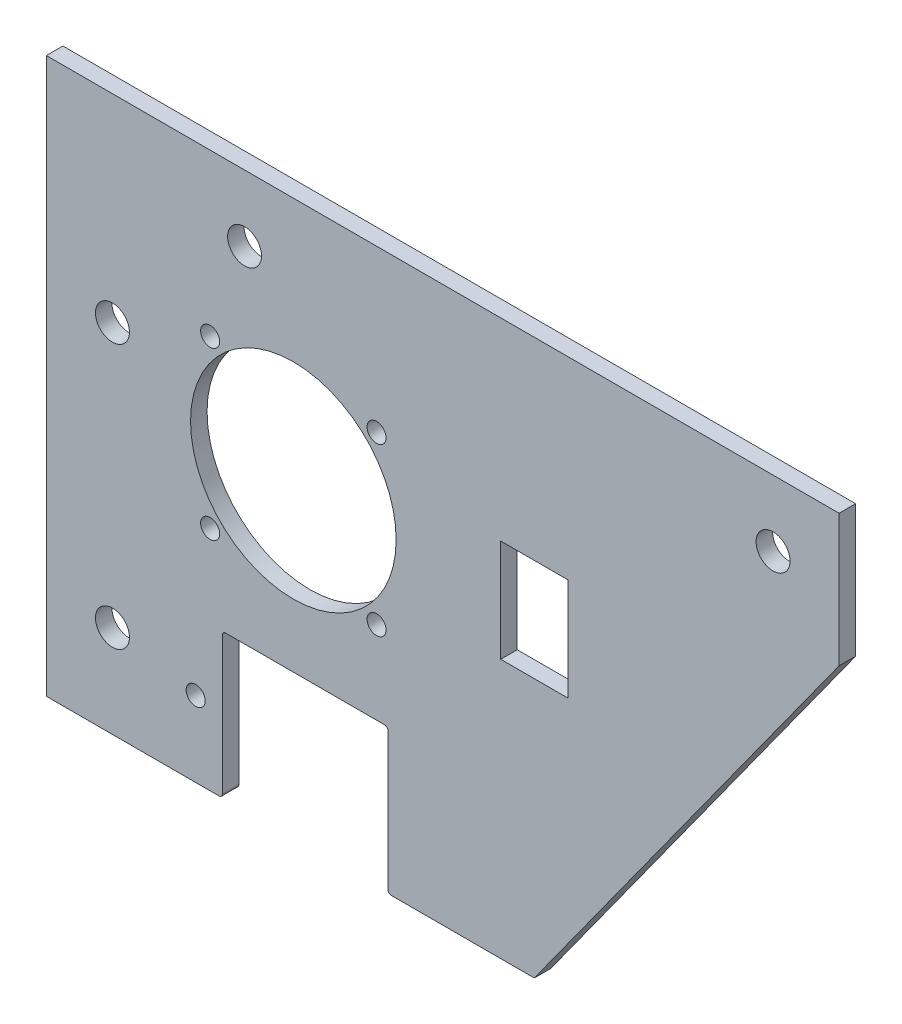
SolidWorks part; units mm, degrees
ref_plane "Front Plane" through (0, 0, 0) normal (0, 0, 1) x (1, 0, 0)
ref_plane "Top Plane" through (0, 0, 0) normal (0, 1, 0) x (1, 0, 0)
ref_plane "Right Plane" through (0, 0, 0) normal (1, 0, 0) x (0, 0, -1)
sketch "Sketch1" plane through (0, 0, 0) normal (0, 0, 1) x (1, 0, 0)
  line L1 (21.5, -40.64) -> (-21.5, -40.64)
  line L2 (21.5, -40.64) -> (21.5, 40.64)
  line L3 (21.5, 40.64) -> (-21.5, 40.64)
  line L4 (-21.5, -40.64) -> (-21.5, 40.64)
  line L5 (21.5, -40.64) -> (-21.5, 40.64) construction
  line L6 (21.5, 40.64) -> (-21.5, -40.64) construction
  line L7 (16.58, 3.04) -> (-15.42, 3.04) construction
  line L8 (16.58, 3.04) -> (16.58, 35.04) construction
  line L9 (16.58, 35.04) -> (-15.42, 35.04) construction
  line L10 (-15.42, 3.04) -> (-15.42, 35.04) construction
  line L11 (16.58, 3.04) -> (-15.42, 35.04) construction
  line L12 (16.58, 35.04) -> (-15.42, 3.04) construction
  line L13 (-12.3, -13.64) -> (18, -13.64)
  line L14 (-12.3, -13.64) -> (-12.3, -37.14)
  line L15 (-12.3, -37.14) -> (18, -37.14)
  line L16 (18, -13.64) -> (18, -37.14)
  line L17 (-12.3, -13.64) -> (18, -37.14) construction
  line L18 (-12.3, -37.14) -> (18, -13.64) construction
  circle A0 centre (0.58, 19.04) radius 19
  circle A1 centre (-15.42, 35.04) radius 1.651
  circle A2 centre (16.58, 35.04) radius 1.651
  circle A3 centre (16.58, 3.04) radius 1.651
  circle A4 centre (-15.42, 3.04) radius 1.651
  circle A5 centre (-18.198, -26.14) radius 1.651
  point P0 (0, 0)
  point P16 (2.85, -25.39)
  dimension "D3" = 38
  dimension "D4" = 2.6
  dimension "D5" = 32
  dimension "D6" = 3.302
  dimension "D7" = 1.92
  dimension "D12" = 3.302
  dimension "D1" = 81.28
  dimension "D2" = 43
  dimension "D8" = 30.3
  dimension "D9" = 23.5
  dimension "D10" = 3.5
  dimension "D11" = 3.5
  dimension "D13" = 3.302
  dimension "D14" = 14.5
sketch "Sketch2" plane through (0, 0, 0) normal (0, 0, 1) x (1, 0, 0)
  line L0 (105.5, 66.04) -> (-46.9, 66.04)
  line L1 (-46.9, 66.04) -> (-46.9, -40.64)
  line L2 (-13.062, -40.64) -> (-13.062, -12.878)
  line L3 (-13.062, -12.878) -> (18.762, -12.878)
  line L4 (21.5, 40.64) -> (-21.5, 40.64) construction
  line L5 (-21.5, -40.64) -> (-21.5, 40.64) construction
  line L6 (21.5, -40.64) -> (-21.5, -40.64) construction
  line L7 (-46.9, -40.64) -> (-13.062, -40.64)
  line L8 (46.9, -40.64) -> (105.5, 40.64)
  line L9 (105.5, 40.64) -> (105.5, 66.04)
  line L10 (21.5, -40.64) -> (21.5, 40.64) construction
  line L11 (-34.2, -40.64) -> (-34.2, 53.34) construction
  line L12 (-34.2, 53.34) -> (105.5, 53.34) construction
  line L13 (18.762, -12.878) -> (18.762, -40.64)
  line L15 (18, -13.64) -> (18, -37.14) construction
  line L16 (-12.3, -13.64) -> (-12.3, -37.14) construction
  line L17 (-12.3, -13.64) -> (18, -13.64) construction
  line L18 (18.762, -40.64) -> (46.9, -40.64)
  line L20 (40.4484, 9.1975) -> (53.3516, 9.1975)
  line L21 (40.4484, 9.1975) -> (40.4484, 28.8825)
  line L22 (40.4484, 28.8825) -> (53.3516, 28.8825)
  line L23 (53.3516, 9.1975) -> (53.3516, 28.8825)
  line L24 (40.4484, 9.1975) -> (53.3516, 28.8825) construction
  line L25 (40.4484, 28.8825) -> (53.3516, 9.1975) construction
  circle A2 centre (0.58, 19.04) radius 19.762
  circle A3 centre (0.58, 19.04) radius 19.762
  point P26 (46.9, 19.04)
  dimension "D8" = 0.762
  dimension "D1" = 25.4
  dimension "D2" = 25.4
  dimension "D3" = 152.4
  dimension "D4" = 25.4
  dimension "D5" = 0.762
  dimension "D6" = 0.762
  dimension "D7" = 0.762
  dimension "D9" = 19.685
  dimension "D10" = 12.9032
extrude "Boss-Extrude1" add sketch "Sketch2" along normal blind 3.175
hole_wizard "#6 Clearance Hole1" positions "Sketch4" profile "Sketch3" hole size "#6" standard "ANSI Inch" end condition through all
sketch "Sketch4" plane through (0, 0, 3.175) normal (0, 0, 1) x (1, 0, 0)
  point P0 (-15.42, 35.04)
  point P3 (16.58, 35.04)
  point P6 (16.58, 3.04)
  point P9 (-15.42, 3.04)
  point P12 (-18.198, -26.14)
sketch "Sketch3" plane through (-15.42, 35.04, 3.175) normal (1, 0, 0) x (0, -1, 0)
  line L0 (0, 0) -> (0, 3.175)
  line L1 (0, 3.175) -> (1.8288, 3.175)
  line L2 (1.8288, 3.175) -> (1.8288, 0)
  line L5 (1.8288, 0) -> (0, 0)
  line L11 (0, -6.35) -> (0, 107.95) construction
  dimension "Thru Hole Dia." = 3.6576
  dimension "Thru Hole Depth" = 3.175
fillet "Fillet1" radius 0.635 4 edges at (-13.062, -40.64, 1.5875) (18.762, -40.64, 1.5875) (18.762, -12.878, 1.5875) (-13.062, -12.878, 1.5875)
hole_wizard "1/4 Clearance Hole1" positions "Sketch6" profile "Sketch5" hole size "1/4" standard "ANSI Inch" end condition through all
sketch "Sketch6" plane through (0, 0, 3.175) normal (0, 0, 1) x (1, 0, 0)
  line L0 (-34.2, -40.64) -> (-34.2, 53.34) construction
  line L1 (-34.2, 53.34) -> (105.5, 53.34) construction
  line L2 (21.5, 40.64) -> (-21.5, 40.64) construction
  line L3 (105.5, 40.64) -> (105.5, 66.04) construction
  line L4 (-21.5, -40.64) -> (-21.5, 40.64) construction
  point P0 (-34.2, -22.86)
  point P4 (-8.8, 53.34)
  point P7 (92.8, 53.34)
  point P15 (-34.2, 27.94)
  dimension "D1" = 12.7
  dimension "D2" = 12.7
  dimension "D3" = 12.7
  dimension "D4" = 50.8
sketch "Sketch5" plane through (-34.2, -22.86, 3.175) normal (1, 0, 0) x (0, -1, 0)
  line L0 (0, 0) -> (0, 3.175)
  line L1 (0, 3.175) -> (3.2639, 3.175)
  line L2 (3.2639, 3.175) -> (3.2639, 0)
  line L5 (3.2639, 0) -> (0, 0)
  line L11 (0, -6.35) -> (0, 107.95) construction
  dimension "Thru Hole Dia." = 6.5278
  dimension "Thru Hole Depth" = 3.175
